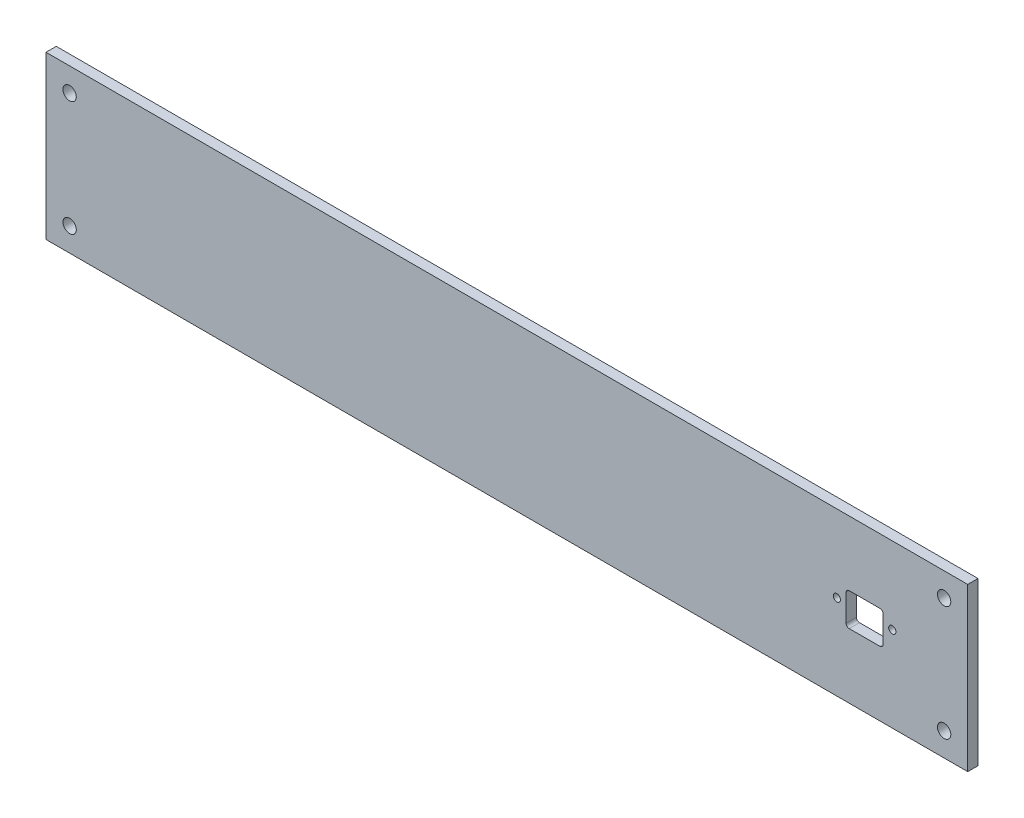
SolidWorks part; units mm, degrees
ref_plane "Piano frontale" through (0, 0, 0) normal (0, 0, 1) x (1, 0, 0)
ref_plane "Piano superiore" through (0, 0, 0) normal (0, 1, 0) x (1, 0, 0)
ref_plane "Piano destro" through (0, 0, 0) normal (1, 0, 0) x (0, 0, -1)
sketch "f" plane through (0, 0, 0) normal (0, 0, 1) x (1, 0, 0)
  line L0 (0, 0) -> (0, 79)
  line L1 (0, 79) -> (449, 79)
  line L2 (449, 79) -> (449, 0)
  line L3 (449, 0) -> (0, 0)
  line L4 (0, 39.5) -> (449, 39.5) construction
  line L5 (224.5, 42) -> (224.5, 123.488) construction
  line L6 (407.7469, 33) -> (407.7469, 46)
  line L7 (406.2469, 47.5) -> (391.2469, 47.5)
  line L8 (389.7469, 46) -> (389.7469, 33)
  line L9 (406.2469, 31.5) -> (391.2469, 31.5)
  line L10 (449, 79) -> (224.5, 0) construction
  line L11 (334, 39.5) -> (334, 81.5) construction
  line L12 (224.5, 0) -> (0, 79) construction
  line L13 (112.25, 42) -> (112.25, 84) construction
  line L14 (383.7289, 41.5) -> (410.6038, 41.5) construction
  line L15 (398.7469, 47.5) -> (398.7469, 31.5) construction
  circle A0 centre (11.5, 67.5) radius 3.25
  circle A1 centre (437.5, 67.5) radius 3.25
  circle A2 centre (11.5, 11.5) radius 3.25
  circle A3 centre (437.5, 11.5) radius 3.25
  circle A4 centre (385.2469, 41.5) radius 1.75
  circle A5 centre (412.2469, 41.5) radius 1.75
  arc A6 (407.7469, 46) -> (406.2469, 47.5) centre (406.2469, 46) ccw
  arc A7 (407.7469, 33) -> (406.2469, 31.5) centre (406.2469, 33) cw
  arc A8 (391.2469, 31.5) -> (389.7469, 33) centre (391.2469, 33) cw
  arc A9 (389.7469, 46) -> (391.2469, 47.5) centre (391.2469, 46) cw
  point P25 (407.7469, 39.5)
  point P26 (389.7469, 39.5)
  point P38 (407.7469, 47.5)
  point P41 (407.7469, 31.5)
  point P44 (389.7469, 31.5)
  point P47 (389.7469, 47.5)
  dimension "D3" = 11.5
  dimension "D4" = 11.5
  dimension "D6" = 18
  dimension "D9" = 2
  dimension "D10" = 1.5
  dimension "D5" = 6.5
  dimension "D8" = 3.5
  dimension "D1" = 79
  dimension "D2" = 449
  dimension "D7" = 8
  dimension "D11" = 13.5
extrude "Estrusione-Estrusione1" add sketch "f" along normal blind 5
